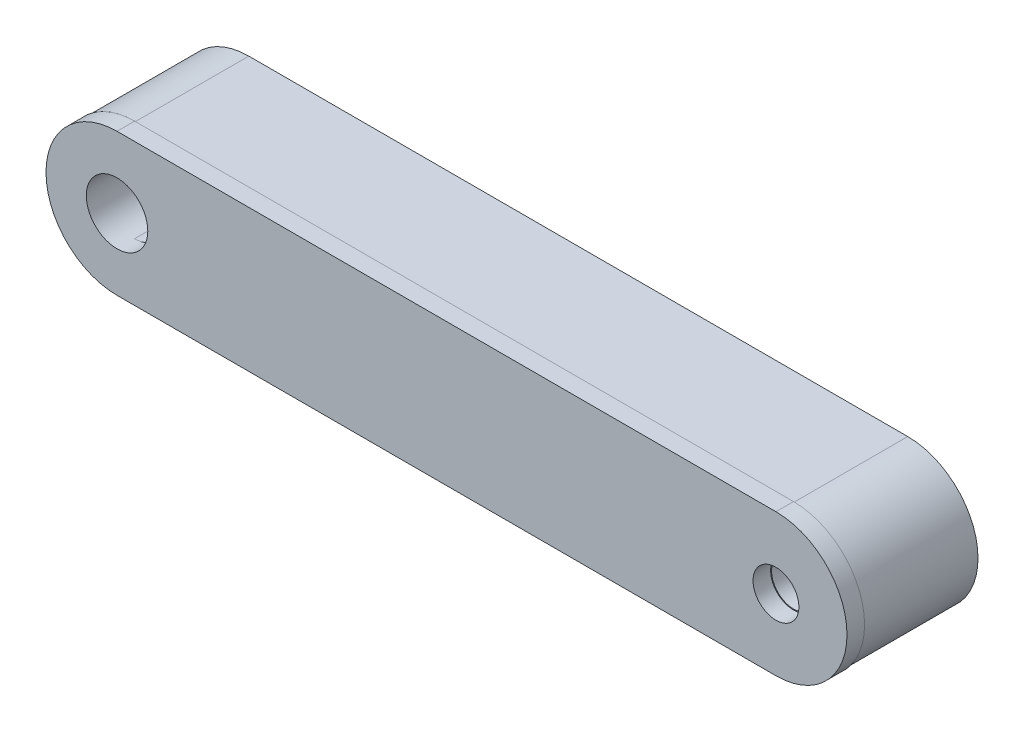
SolidWorks part; units mm, degrees
ref_plane "Front Plane" through (0, 0, 0) normal (0, 0, 1) x (1, 0, 0)
ref_plane "Top Plane" through (0, 0, 0) normal (0, 1, 0) x (1, 0, 0)
ref_plane "Right Plane" through (0, 0, 0) normal (1, 0, 0) x (0, 0, -1)
sketch "Sketch1" plane through (0, 0, 0) normal (0, 0, 1) x (1, 0, 0)
  line L0 (-89.7683, 37.336) -> (-14.7683, 37.336) construction
  line L1 (-89.7683, 45.3335) -> (-14.7683, 45.3335)
  line L2 (-89.7683, 29.3384) -> (-14.7683, 29.3384)
  line L3 (-89.7683, 40.836) -> (-77.7683, 40.836)
  line L4 (-89.7683, 33.836) -> (-77.7683, 33.836)
  arc A0 (-89.7683, 45.3335) -> (-89.7683, 29.3384) centre (-89.7683, 37.336) ccw
  arc A1 (-14.7683, 29.3384) -> (-14.7683, 45.3335) centre (-14.7683, 37.336) ccw
  circle A2 centre (-14.7683, 37.336) radius 2.5
  arc A3 (-89.7683, 40.836) -> (-89.7683, 33.836) centre (-89.7683, 37.336) ccw
  arc A4 (-77.7683, 40.836) -> (-77.7683, 33.836) centre (-77.7683, 37.336) cw
  point P2 (-52.2683, 37.336)
  dimension "D1" = 75
extrude "Boss-Extrude1" add sketch "Sketch1" along normal blind 13
sketch "Sketch2" plane through (0, 0, 13) normal (0, 0, 1) x (1, 0, 0)
  line L0 (-89.7683, 37.336) -> (-14.7683, 37.336) construction
  line L1 (-89.7683, 45.4223) -> (-14.7683, 45.4223)
  line L2 (-89.7683, 29.2496) -> (-14.7683, 29.2496)
  arc A0 (-89.7683, 45.4223) -> (-89.7683, 29.2496) centre (-89.7683, 37.336) ccw
  arc A1 (-14.7683, 29.2496) -> (-14.7683, 45.4223) centre (-14.7683, 37.336) ccw
  circle A2 centre (-14.7683, 37.336) radius 2.6099
  circle A3 centre (-89.7683, 37.336) radius 3.5
  point P4 (-52.2683, 37.336)
extrude "Boss-Extrude2" add sketch "Sketch2" along normal blind 2
